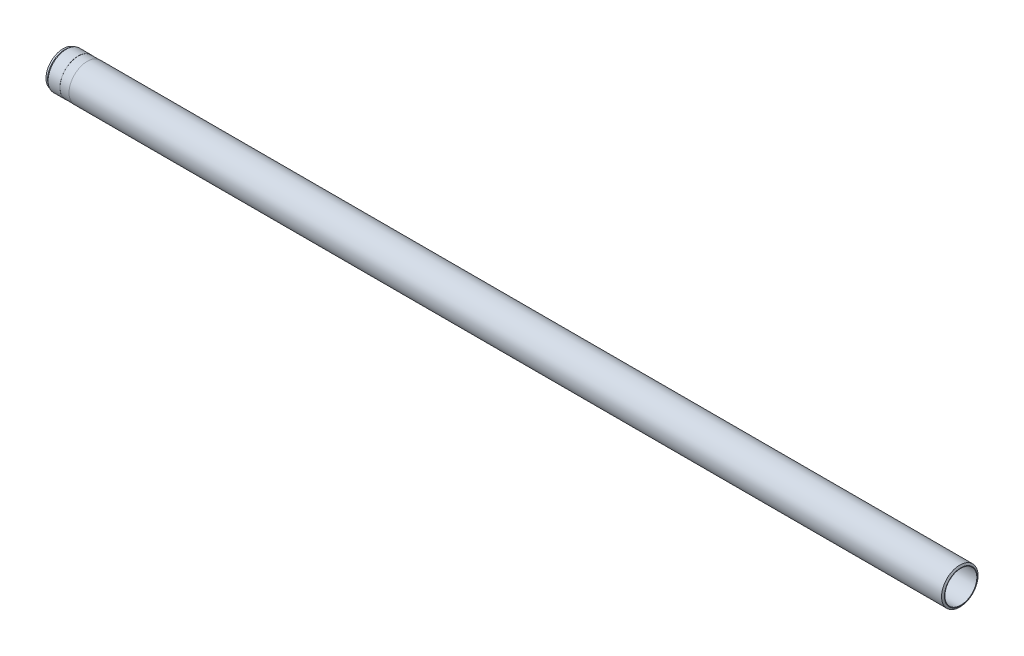
SolidWorks part; units mm, degrees
ref_plane "Front" through (0, 0, 0) normal (0, 0, 1) x (1, 0, 0)
ref_plane "Top" through (0, 0, 0) normal (0, 1, 0) x (1, 0, 0)
ref_plane "Right" through (0, 0, 0) normal (1, 0, 0) x (0, 0, -1)
sketch "Sketch1" plane through (0, 0, 0) normal (0, 0, 1) x (1, 0, 0)
  line L0 (-122.7842, 0) -> (99.5499, 0) construction
  line L1 (0, 35) -> (0, 36)
  line L2 (0, 36) -> (-2.3094, 40)
  line L3 (-2.3094, 40) -> (-1915, 40)
  line L4 (-1915, 40) -> (-1915, 39.75)
  line L5 (-1915, 39.75) -> (-1935, 39.75)
  line L6 (-1935, 39.75) -> (-1935, 40)
  line L7 (-1935, 40) -> (-1960.9296, 40)
  line L8 (-1960.9296, 40) -> (-1964.5, 37.5)
  line L9 (-1964.5, 37.5) -> (-1968, 37.5)
  line L10 (-1968, 37.5) -> (-1968, 35.7274)
  line L11 (-1968, 35.7274) -> (-1967, 35.15)
  line L12 (-1967, 35.15) -> (-1953, 35.15)
  line L13 (-1953, 35.15) -> (-1952.7402, 35)
  line L14 (-1952.7402, 35) -> (0, 35)
  dimension "D1" = 1968
  dimension "D2" = 80
  dimension "D3" = 70
  dimension "D4" = 70.3
  dimension "D5" = 75
  dimension "D6" = 72
  dimension "D7" = 60
  dimension "D8" = 79.5
  dimension "D9" = 3.5
  dimension "D10" = 35
  dimension "D11" = 30
  dimension "D12" = 1
  dimension "D13" = 30
  dimension "D14" = 15
  dimension "D15" = 33
  dimension "D16" = 20
revolve "Base-Revolve" add sketch "Sketch1" angle 360 about L0
